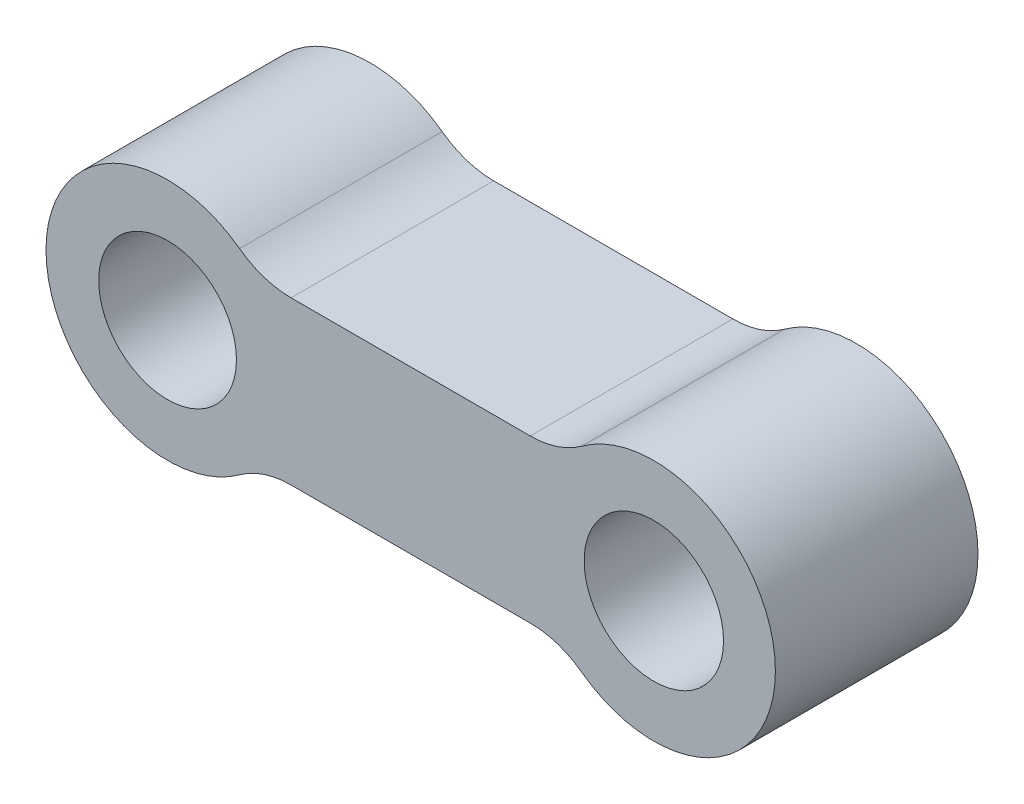
SolidWorks part; units mm, degrees
ref_plane "Alzado" through (0, 0, 0) normal (0, 0, 1) x (1, 0, 0)
ref_plane "Planta" through (0, 0, 0) normal (0, 1, 0) x (1, 0, 0)
ref_plane "Vista lateral" through (0, 0, 0) normal (1, 0, 0) x (0, 0, -1)
sketch "Croquis1" plane through (0, 0, 0) normal (0, 0, 1) x (1, 0, 0)
  line L0 (-15, 0) -> (15, 0) construction
  line L1 (0, 8.3888) -> (0, 0) construction
  line L2 (-7.3777, -5) -> (7.3777, -5)
  line L3 (-7.3777, 5) -> (7.3777, 5)
  circle A0 centre (-15, 0) radius 4.25
  arc A1 (-10.5581, 6.0431) -> (-10.5581, -6.0431) centre (-15, 0) ccw
  arc A2 (10.5581, -6.0431) -> (10.5581, 6.0431) centre (15, 0) ccw
  circle A3 centre (15, 0) radius 4.3
  arc A4 (-10.5581, 6.0431) -> (-7.3777, 5) centre (-7.3777, 10.3699) ccw
  arc A5 (10.5581, 6.0431) -> (7.3777, 5) centre (7.3777, 10.3699) cw
  arc A6 (10.5581, -6.0431) -> (7.3777, -5) centre (7.3777, -10.3699) ccw
  arc A7 (-10.5581, -6.0431) -> (-7.3777, -5) centre (-7.3777, -10.3699) cw
  point P3 (0, 0)
  dimension "D2" = 15
  dimension "D4" = 8.5
  dimension "D5" = 8.6
  dimension "D6" = 5
  dimension "D1" = 30
extrude "Saliente-Extruir1" add sketch "Croquis1" along normal blind 12.5
